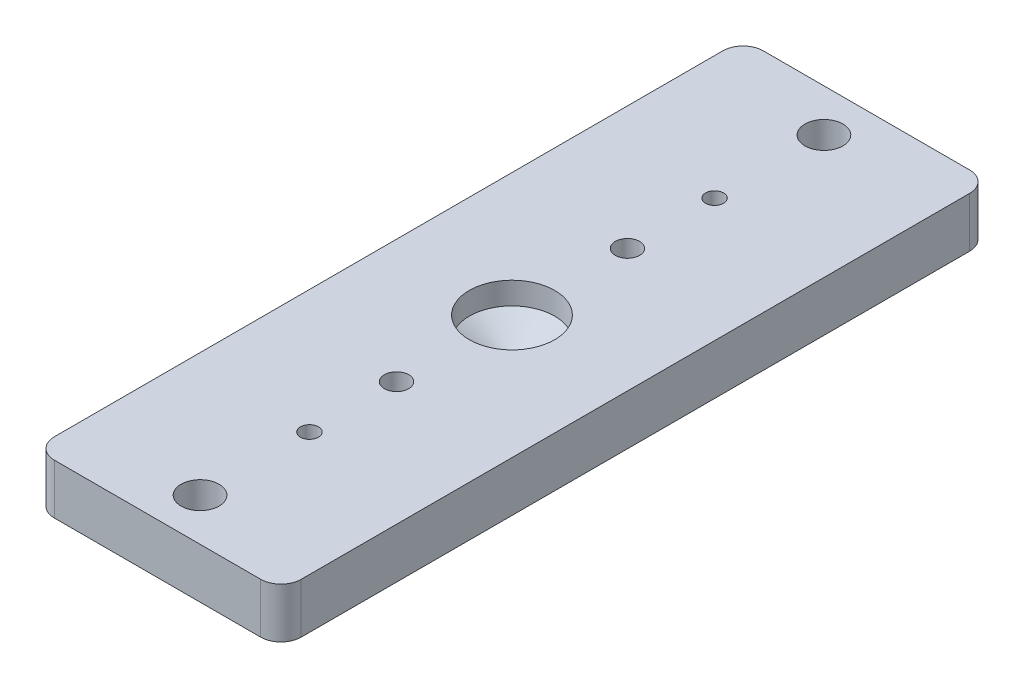
SolidWorks part; units mm, degrees
material "6061-T6 (SS)"
ref_plane "Front Plane" through (0, 0, 0) normal (0, 0, 1) x (1, 0, 0)
ref_plane "Top Plane" through (0, 0, 0) normal (0, 1, 0) x (1, 0, 0)
ref_plane "Right Plane" through (0, 0, 0) normal (1, 0, 0) x (0, 0, -1)
sketch "Sketch1" plane through (0, 0, 0) normal (0, 1, 0) x (1, 0, 0)
  line L0 (-15.4781, -44.45) -> (-15.4781, 44.45)
  line L1 (15.4781, 44.45) -> (15.4781, -44.45)
  line L2 (-15.4781, 0) -> (15.4781, 0) construction
  line L3 (0, 41.275) -> (0, -41.275) construction
  line L4 (-15.4781, 44.45) -> (15.4781, 44.45)
  line L5 (-15.4781, -44.45) -> (15.4781, -44.45)
  dimension "D2" = 30.9562
  dimension "D1" = 88.9
extrude "Boss-Extrude1" add sketch "Sketch1" along normal blind 4.7625
fillet "Fillet1" radius 2.54 4 edges at (15.4781, 2.3813, -44.45) (-15.4781, 2.3813, -44.45) (15.4781, 2.3813, 44.45) (-15.4781, 2.3813, 44.45)
sketch "Sketch6" plane through (0, 0, 0) normal (0, -1, 0) x (1, 0, 0)
  line L0 (0, 0) -> (-28.2073, 0) construction
  line L1 (-12.9381, 44.45) -> (12.9381, 44.45) construction
  circle A0 centre (0, 14.478) radius 1.524
  circle A1 centre (0, -14.478) radius 1.524
  point P9 (0, 44.45)
  dimension "D1" = 3.048
  dimension "D2" = 14.478
extrude "Cut-Extrude1" cut sketch "Sketch6" against normal through all
sketch "Sketch7" plane through (0, 0, 0) normal (0, -1, 0) x (1, 0, 0)
  line L1 (12.9381, -44.45) -> (-12.9381, -44.45) construction
  line L2 (0, 0) -> (-19.1679, 0) construction
  circle A0 centre (0, -39.116) radius 2.3812
  circle A1 centre (0, 39.116) radius 2.3812
  dimension "D1" = 4.7625
  dimension "D2" = 5.334
extrude "Cut-Extrude2" cut sketch "Sketch7" against normal through all
sketch "Sketch9" plane through (0, 0, 0) normal (0, -1, 0) x (1, 0, 0)
  line L0 (12.9381, -44.45) -> (-12.9381, -44.45) construction
  line L1 (15.4781, 41.91) -> (15.4781, -41.91) construction
  line L2 (-15.4781, -41.91) -> (-15.4781, 41.91) construction
  line L3 (-12.9381, 44.45) -> (12.9381, 44.45) construction
  line L4 (12.9381, -44.45) -> (-12.9381, -44.45)
  line L5 (15.4781, 41.91) -> (15.4781, -41.91)
  line L6 (-15.4781, -41.91) -> (-15.4781, 41.91)
  line L7 (-12.9381, 44.45) -> (12.9381, 44.45)
  arc A0 (12.9381, -44.45) -> (15.4781, -41.91) centre (12.9381, -41.91) ccw construction
  arc A1 (-15.4781, -41.91) -> (-12.9381, -44.45) centre (-12.9381, -41.91) ccw construction
  arc A2 (15.4781, 41.91) -> (12.9381, 44.45) centre (12.9381, 41.91) ccw construction
  arc A3 (-12.9381, 44.45) -> (-15.4781, 41.91) centre (-12.9381, 41.91) ccw construction
  arc A4 (12.9381, -44.45) -> (15.4781, -41.91) centre (12.9381, -41.91) ccw
  arc A5 (-15.4781, -41.91) -> (-12.9381, -44.45) centre (-12.9381, -41.91) ccw
  arc A6 (15.4781, 41.91) -> (12.9381, 44.45) centre (12.9381, 41.91) ccw
  arc A7 (-12.9381, 44.45) -> (-15.4781, 41.91) centre (-12.9381, 41.91) ccw
extrude "Boss-Extrude3" add sketch "Sketch9" along normal blind 1.524
hole_wizard "#4-40 Tapped Hole1" positions "Sketch5" profile "Sketch4" tap size "#4-40" standard "Ansi Inch" end condition through all
sketch "Sketch5" plane through (0, 4.7625, 0) normal (0, 1, 0) x (-1, 0, 0)
  line L0 (0, 0) -> (16.1552, 0) construction
  point P0 (0, 25.4)
  point P9 (0, -25.4)
  dimension "D1" = 50.8
sketch "Sketch4" plane through (0, 4.7625, 25.4) normal (1, 0, 0) x (0, 0, 1)
  line L0 (0, 0) -> (0, 6.2865)
  line L1 (0, 6.2865) -> (1.1303, 6.2865)
  line L2 (1.1303, 6.2865) -> (1.1303, 0)
  line L5 (1.1303, 0) -> (0, 0)
  line L11 (0, -6.35) -> (0, 107.95) construction
  dimension "Thread Major Dia." = 2.2606
  dimension "Thru Tap Drill Depth" = 6.2865
sketch "Sketch10" plane through (0, 0, 0) normal (0, 1, 0) x (1, 0, 0)
  circle A0 centre (0, -14.478) radius 1.524 construction
  circle A1 centre (0, 14.478) radius 1.524 construction
  circle A2 centre (0, -14.478) radius 1.524
  circle A3 centre (0, 14.478) radius 1.524
extrude "Cut-Extrude3" cut sketch "Sketch10" against normal through all
sketch "Sketch11" plane through (0, -1.524, 0) normal (0, -1, 0) x (1, 0, 0)
  line L0 (0, 0) -> (-8.2063, 0) construction
  circle A0 centre (0, -14.478) radius 3.175
  circle A1 centre (0, 14.478) radius 3.175
  dimension "D1" = 6.35
extrude "Cut-Extrude4" cut sketch "Sketch11" against normal blind 3.302
hole_wizard "1/2-13 Tapped Hole2" positions "Sketch15" profile "Sketch14" tap size "1/2-13" standard "Ansi Inch"
sketch "Sketch15" plane through (0, 4.7625, 0) normal (0, 1, 0) x (-1, 0, 0)
  point P0 (0, 0)
sketch "Sketch14" plane through (0, 4.7625, 0) normal (1, 0, 0) x (0, 0, 1)
  line L0 (0, 0) -> (0, 6.0135)
  line L1 (0, 6.0135) -> (5.3581, 2.794)
  line L2 (5.3581, 2.794) -> (5.3581, 0)
  line L5 (5.3581, 0) -> (0, 0)
  line L10 (0, 6.0135) -> (-5.3581, 2.794) construction
  line L11 (0, -6.35) -> (0, 107.95) construction
  dimension "Tap Drill Dia." = 10.7163
  dimension "Tap Drill Depth" = 2.794
  dimension "Drill Angle" = 118
cosmetic thread "Hole Thread2" parameters "D1"=2.794, "D2"=12.7
